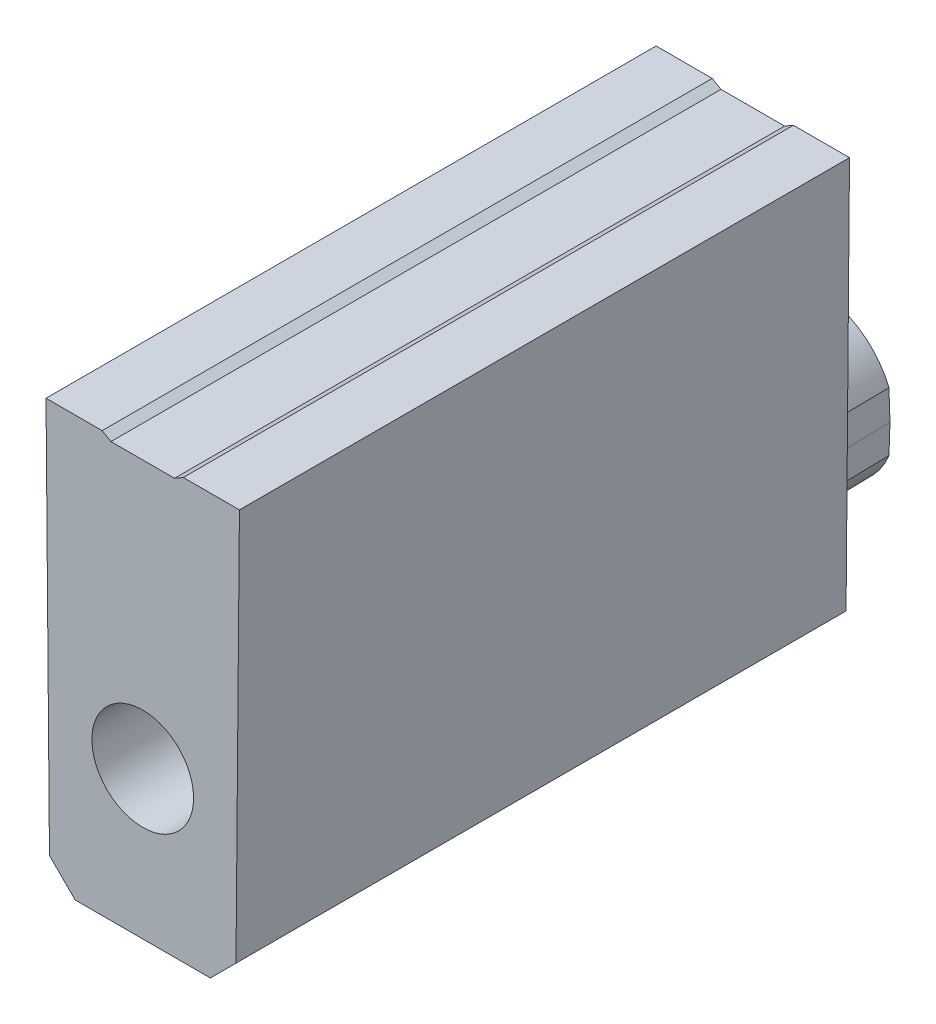
SolidWorks part; units mm, degrees
ref_plane "Front Plane" through (0, 0, 0) normal (0, 0, 1) x (1, 0, 0)
ref_plane "Top Plane" through (0, 0, 0) normal (0, 1, 0) x (1, 0, 0)
ref_plane "Right Plane" through (0, 0, 0) normal (1, 0, 0) x (0, 0, -1)
sketch "Sketch1" plane through (0, 0, 0) normal (0, 0, 1) x (1, 0, 0)
  line L0 (-2.3241, 0) -> (2.3241, 0)
  line L1 (2.3241, 0) -> (2.4156, 10.4902)
  line L2 (2.4156, 10.4902) -> (-2.4156, 10.4902)
  line L3 (-2.4156, 10.4902) -> (-2.3241, 0)
  point P3 (0, 10.4902)
  dimension "D1" = 1
  dimension "D2" = 4.6482
  dimension "D3" = 10.4902
extrude "Extrude1" add sketch "Sketch1" along normal blind 15.24
sketch "Sketch2" plane through (0, 0, 0) normal (0, 0, -1) x (-1, 0, 0)
  line L0 (-2.6028, 3.683) -> (2.7968, 3.683) construction
  line L1 (-1.841, 4.4235) -> (-1.8669, 3.683)
  line L2 (-1.8669, 3.683) -> (-1.841, 2.9425)
  line L3 (1.841, 4.4235) -> (1.8669, 3.683)
  line L4 (1.8669, 3.683) -> (1.841, 2.9425)
  arc A0 (-1.841, 2.9425) -> (1.841, 2.9425) centre (0, 3.683) ccw
  arc A1 (1.841, 4.4235) -> (-1.841, 4.4235) centre (0, 3.683) ccw
  dimension "D1" = 3.9688
  dimension "D2" = 3.683
  dimension "D3" = 92
  dimension "D4" = 92
  dimension "D5" = 3.7338
extrude "Extrude2" add sketch "Sketch2" along normal blind 1.5875 draft 1
sketch "Sketch3" plane through (0, 0, 15.24) normal (0, 0, 1) x (1, 0, 0)
  circle A0 centre (0, 3.683) radius 1.27
  dimension "D1" = 2.54
extrude "Extrude3" cut sketch "Sketch3" against normal blind 8.89 draft 0.5
sketch "Sketch4" plane through (0, 0, 0) normal (0, 0, -1) x (-1, 0, 0)
  line L0 (-1.0137, 10.4902) -> (-0.7937, 10.3632)
  line L1 (-2.4156, 10.4902) -> (2.4156, 10.4902) construction
  line L2 (-0.7937, 10.3632) -> (0.7937, 10.3632)
  line L3 (0.7937, 10.3632) -> (1.0137, 10.4902)
  line L4 (1.0137, 10.4902) -> (-1.0137, 10.4902)
  point P4 (0, 10.3632)
  point P7 (0, 10.4902)
  dimension "D1" = 1.5875
  dimension "D2" = 120
  dimension "D3" = 0.127
extrude "Extrude4" cut sketch "Sketch4" against normal through all
sketch "Sketch5" plane through (0, 0, 0) normal (0, 0, -1) x (-1, 0, 0)
  line L0 (-1.6891, 0) -> (-2.3297, 0.6406)
  line L1 (2.3241, 0) -> (-2.3241, 0) construction
  line L2 (-2.3241, 0) -> (-2.4156, 10.4902) construction
  line L3 (-2.3297, 0.6406) -> (-2.3241, 0)
  line L4 (-2.3241, 0) -> (-1.6891, 0)
  line L5 (2.3241, 0) -> (1.6891, 0)
  line L6 (1.6891, 0) -> (2.3297, 0.6406)
  line L7 (2.4156, 10.4902) -> (2.3241, 0) construction
  line L8 (2.3297, 0.6406) -> (2.3241, 0)
  dimension "D1" = 45
  dimension "D2" = 0.635
  dimension "D3" = 45
extrude "Cut-Extrude1" cut sketch "Sketch5" against normal through all
